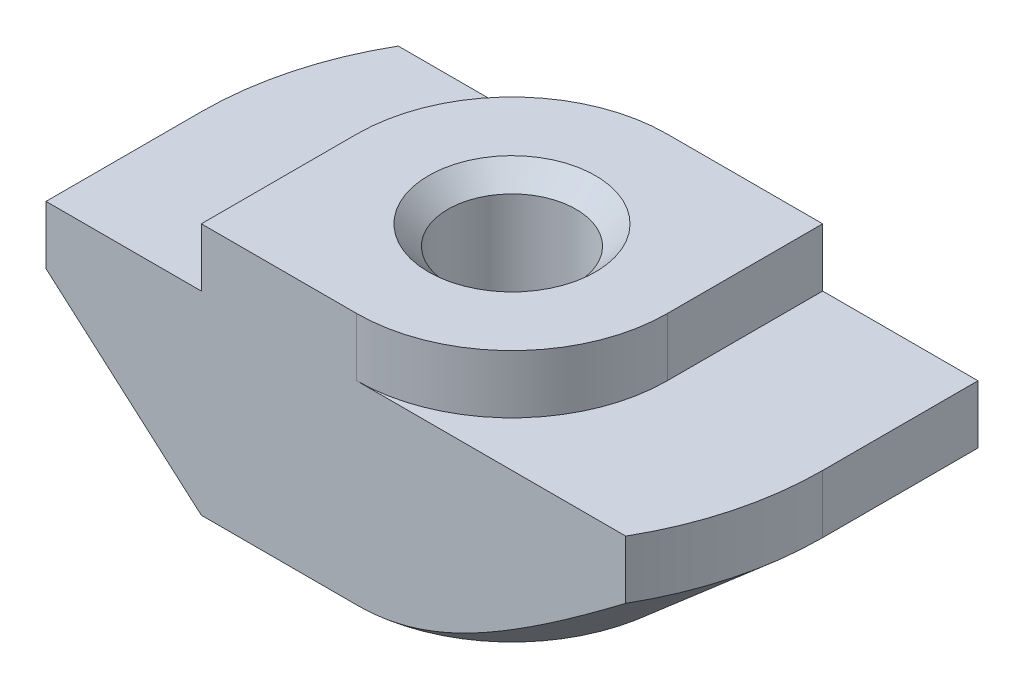
SolidWorks part; units mm, degrees
material "Сталь 20  ГОСТ 1050-2013"
ref_plane "Спереди" through (0, 0, 0) normal (0, 0, 1) x (1, 0, 0)
ref_plane "Сверху" through (0, 0, 0) normal (0, 1, 0) x (1, 0, 0)
ref_plane "Справа" through (0, 0, 0) normal (1, 0, 0) x (0, 0, -1)
sketch "Эскиз1" plane through (0, 0, 0) normal (0, 0, 1) x (1, 0, 0)
  line L0 (4, 0) -> (-4, 0)
  line L1 (-4, 0) -> (-4, -1.5)
  line L2 (-4, -1.5) -> (-8, -1.5)
  line L3 (-8, -1.5) -> (-8, -6.5)
  line L4 (-8, -6.5) -> (8, -6.5)
  line L5 (0, -6.5) -> (0, 0) construction
  line L6 (8, -1.5) -> (8, -6.5)
  line L7 (4, -1.5) -> (8, -1.5)
  line L8 (4, 0) -> (4, -1.5)
  dimension "D1" = 8
  dimension "D2" = 16
  dimension "D3" = 6.5
  dimension "D4" = 1.5
extrude "Бобышка-Вытянуть1" add sketch "Эскиз1" along normal mid plane 8
hole_wizard "Отверстие обработанное метчиком M42" positions "Эскиз2" profile "Эскиз3" tap size "M4" standard "ISO" end condition up to next
sketch "Эскиз2" plane through (0, 0, 0) normal (0, 1, 0) x (1, 0, 0)
  point P0 (0, 0)
sketch "Эскиз3" plane through (0, 0, 0) normal (1, 0, 0) x (0, 0, 1)
  line L0 (0, 0) -> (0, 6.5)
  line L1 (0, 6.5) -> (2.15, 6.5)
  line L2 (1.65, 6) -> (1.65, 0.5)
  line L3 (1.65, 0.5) -> (2.15, 0)
  line L5 (2.15, 0) -> (0, 0)
  line L6 (-1.65, 0.5) -> (-2.15, 0) construction
  line L7 (2.15, 6.5) -> (1.65, 6)
  line L8 (-2.15, 6.5) -> (-1.65, 6) construction
  line L11 (0, -6.35) -> (0, 107.95) construction
  dimension "Диаметр проходного сверла" = 3.3
  dimension "Глубина проходного сверла" = 6.5
  dimension "Диаметр передней зенковки" = 4.3
  dimension "Угол передней зенковки" = 90
  dimension "Диаметр задней зенковки" = 4.3
  dimension "Угол задней зенковки" = 90
cosmetic thread "Отверстие резьбы1" parameters "D2"=4
sketch "Эскиз4" plane through (0, 0, 0) normal (0, 1, 0) x (1, 0, 0)
  line L0 (-4, 4) -> (-4, 0)
  line L1 (-4, -4) -> (-4, 4) construction
  line L2 (4, 4) -> (-4, 4) construction
  line L3 (0, 4) -> (-4, 4)
  line L4 (0, -4) -> (4, -4)
  line L5 (4, -4) -> (-4, -4) construction
  line L6 (4, -4) -> (4, 0)
  line L7 (4, -4) -> (4, 4) construction
  arc A0 (-4, 0) -> (0, 4) centre (0, 0) cw
  arc A1 (4, 0) -> (0, -4) centre (0, 0) cw
extrude "Вырез-Вытянуть1" cut sketch "Эскиз4" against normal up to surface (1.5 mm away) up to face at (-6, -1.5, 0)
sketch "Эскиз5" plane through (0, -1.5, 0) normal (0, 1, 0) x (1, 0, 0)
  line L0 (-8, 0) -> (-8, 4)
  line L1 (-8, -4) -> (-8, 4) construction
  line L2 (-8, 4) -> (-6.9282, 4)
  line L3 (0, 4) -> (-8, 4) construction
  line L4 (8, 0) -> (8, -4)
  line L5 (8, -4) -> (8, 4) construction
  line L6 (8, -4) -> (6.9282, -4)
  line L7 (8, -4) -> (0, -4) construction
  arc A0 (-6.9282, 4) -> (-8, 0) centre (0, 0) ccw
  arc A2 (8, 0) -> (6.9282, -4) centre (0, 0) cw
  point P19 (0, 0)
extrude "Вырез-Вытянуть2" cut sketch "Эскиз5" against normal through all
sketch "Эскиз6" plane through (0, 0, 4) normal (0, 0, 1) x (1, 0, 0)
  line L0 (-8, -3) -> (-8, -6.5)
  line L1 (-8, -1.5) -> (-8, -6.5) construction
  line L2 (-8, -6.5) -> (-4, -6.5)
  line L3 (-8, -6.5) -> (6.9282, -6.5) construction
  line L4 (-4, -6.5) -> (-8, -3)
  line L5 (-4, -1.5) -> (-8, -1.5) construction
  line L6 (-4, 0) -> (-4, -1.5) construction
  point P10 (0, 0)
  dimension "D1" = 1.5
sketch "Эскиз7" plane through (0, -6.5, 0) normal (0, -1, 0) x (1, 0, 0)
  line L0 (0, 8) -> (-8, 8)
  line L1 (-8, 8) -> (-8, 0)
  line L2 (0, -8) -> (8, -8)
  line L3 (8, -8) -> (8, 0)
  arc A0 (-8, 0) -> (0, -8) centre (0, 0) ccw
  arc A1 (8, 0) -> (0, 8) centre (0, 0) ccw
sweep "Вырез-По траектории1" cut profiles "Эскиз6" path "Эскиз7"
